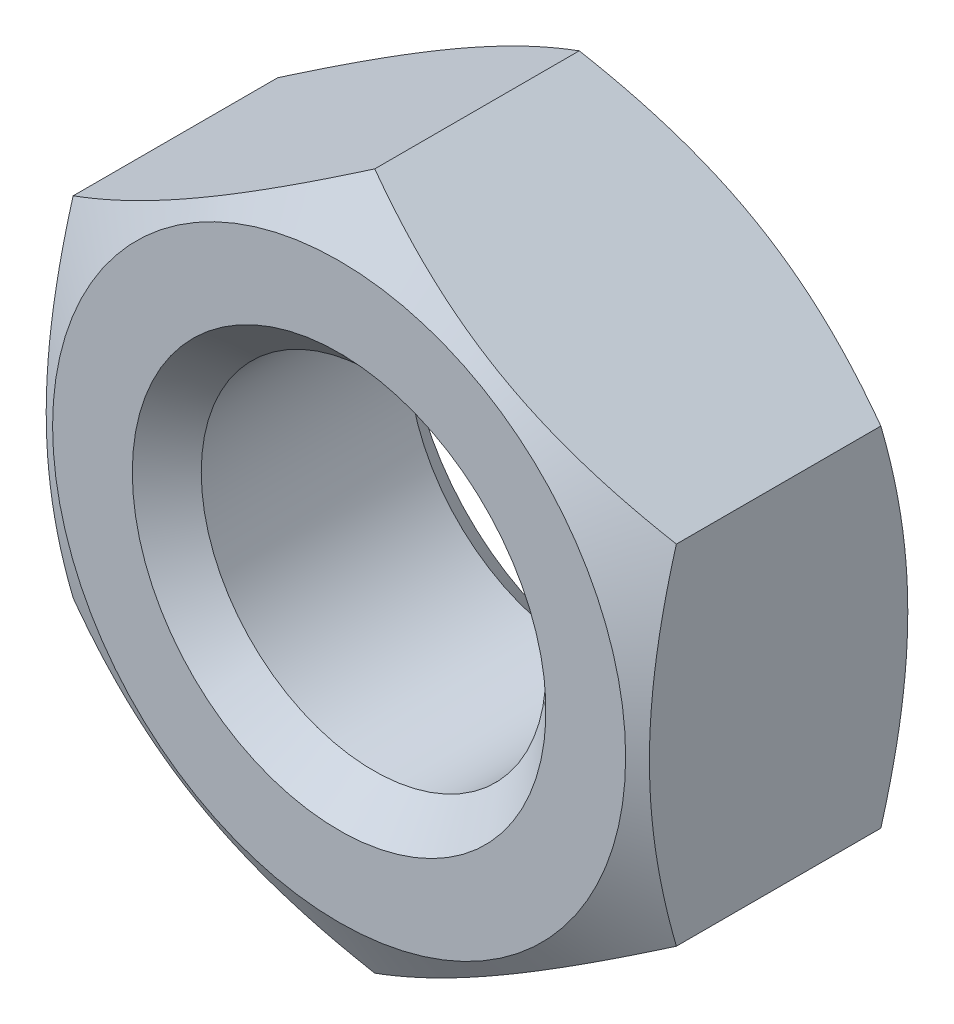
SolidWorks part; units mm, degrees
material "Простая углеродистая сталь"
ref_plane "Спереди" through (0, 0, 0) normal (0, 0, 1) x (1, 0, 0)
ref_plane "Сверху" through (0, 0, 0) normal (0, 1, 0) x (1, 0, 0)
ref_plane "Справа" through (0, 0, 0) normal (1, 0, 0) x (0, 0, -1)
sketch "Эскиз1" plane through (0, 0, 0) normal (0, 1, 0) x (1, 0, 0)
  line L1 (0, 0) -> (-5, 0)
  line L2 (0, 0) -> (0, 3.2)
  line L3 (0, 3.2) -> (-5, 3.2)
  line L4 (-5, 0) -> (-5, 3.2)
  dimension "D1" = 3.2
  dimension "D2" = 5
revolve "Повернуть1" add sketch "Эскиз1" angle 360 about L2
sketch "Эскиз2" plane through (0, 0, 0) normal (0, 0, 1) x (1, 0, 0)
  line L7 (3.5, -2.0207) -> (3.5, 2.0207)
  line L8 (3.5, 2.0207) -> (0, 4.0415)
  line L9 (0, 4.0415) -> (-3.5, 2.0207)
  line L10 (-3.5, 2.0207) -> (-3.5, -2.0207)
  line L11 (-3.5, -2.0207) -> (0, -4.0415)
  line L12 (0, -4.0415) -> (3.5, -2.0207)
  circle A0 centre (0, 0) radius 3.5 construction
  dimension "D1" = 3.5
extrude "Вырез-Вытянуть1" cut sketch "Эскиз2" against normal up to surface (3.2 mm away) flip side to cut up to face at (5, 0, -3.2)
sketch "Эскиз3" plane through (0, 0, 0) normal (0, 0, 1) x (1, 0, 0)
  circle A0 centre (0, 0) radius 2
  dimension "D1" = 4
extrude "Вырез-Вытянуть2" cut sketch "Эскиз3" against normal through all both and the other way through all
sketch "Эскиз4" plane through (0, 0, 0) normal (1, 0, 0) x (0, 0, -1)
  line L0 (0, 3.325) -> (0.4136, 4.0415)
  line L1 (0, 2.0207) -> (0, 4.0415) construction
  line L2 (3.2, 4.0415) -> (0, 4.0415) construction
  line L3 (0.4136, 4.0415) -> (0, 4.0415)
  line L4 (0, 4.0415) -> (0, 3.325)
  line L5 (1.6, 8.7184) -> (1.6, -2.1993) construction
  line L6 (3.2, 3.325) -> (2.7864, 4.0415)
  line L7 (3.2, 4.0415) -> (3.2, 3.325)
  line L8 (2.7864, 4.0415) -> (3.2, 4.0415)
  line L9 (0, 0) -> (50000, 0) construction
  dimension "D1" = 3.325
  dimension "D2" = 30
  dimension "D3" = 1.6
revolve "Вырез-Повернуть1" cut sketch "Эскиз4" angle 360 about L9
chamfer "Фаска1" distance 0.4 angle 45 2 edges at (-2, 0, 0) (2, 0, -3.2)
